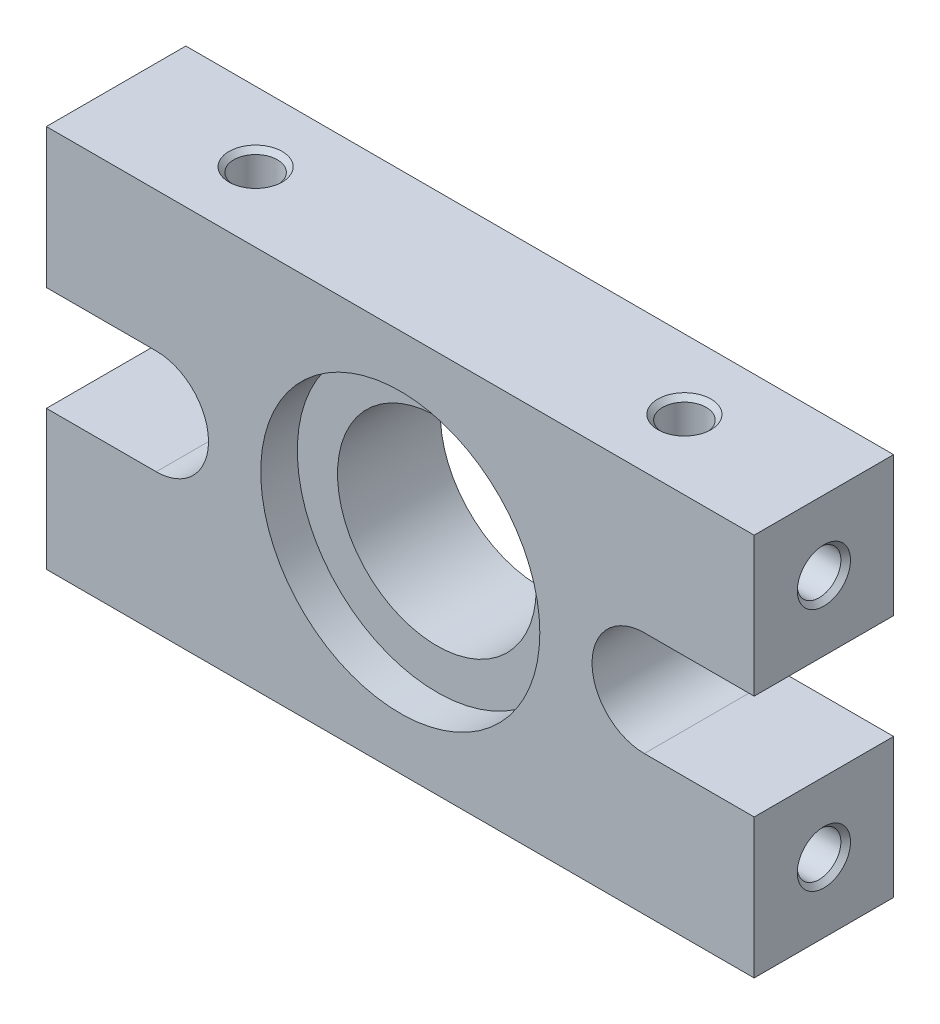
SolidWorks part; units mm, degrees
material "1060 Alloy"
ref_plane "Front Plane" through (0, 0, 0) normal (0, 0, 1) x (1, 0, 0)
ref_plane "Top Plane" through (0, 0, 0) normal (0, 1, 0) x (1, 0, 0)
ref_plane "Right Plane" through (0, 0, 0) normal (1, 0, 0) x (0, 0, -1)
sketch "Sketch1" plane through (0, 0, 0) normal (0, 0, 1) x (1, 0, 0)
  line L0 (0, 14) -> (0, 22)
  line L1 (0, 0) -> (40.6, 0)
  line L2 (0, 0) -> (0, 8)
  line L3 (0, 22) -> (40.6, 22)
  line L4 (40.6, 0) -> (40.6, 8)
  line L5 (0, 14) -> (6.3, 14)
  line L7 (0, 8) -> (6.3, 8)
  line L8 (40.6, 8) -> (34.3, 8)
  line L9 (40.6, 14) -> (34.3, 14)
  line L10 (40.6, 14) -> (40.6, 22)
  arc A0 (6.3, 8) -> (6.3, 14) centre (6.3, 11) ccw
  arc A1 (34.3, 8) -> (34.3, 14) centre (34.3, 11) cw
  circle A2 centre (20.3, 11) radius 5.7
  dimension "D3" = 6
  dimension "D5" = 11
  dimension "D7" = 11.4
  dimension "D1" = 40.6
  dimension "D2" = 22
  dimension "D4" = 6.3
  dimension "D6" = 6
extrude "Boss-Extrude1" add sketch "Sketch1" along normal blind 8
sketch "Sketch2" plane through (0, 0, 8) normal (0, 0, 1) x (1, 0, 0)
  circle A0 centre (20.3, 11) radius 8.005
  dimension "D1" = 16.01
extrude "Cut-Extrude1" cut sketch "Sketch2" against normal blind 2.1
ref_plane "Plane1" through (20.3, 0, 0) normal (1, 0, 0) x (0, 0, -1)
ref_plane "Plane2" through (0, 11, 0) normal (0, -1, 0) x (-1, 0, 0)
hole_wizard "M3x0.5 Tapped Hole1" positions "Sketch4" profile "Sketch3" tap size "M3x0.5" standard "ANSI Metric"
sketch "Sketch4" plane through (0, 22, 0) normal (0, 1, 0) x (1, 0, 0)
  line L0 (40.6, -8) -> (40.6, 0) construction
  line L1 (40.6, 0) -> (0, 0) construction
  point P0 (32.6, -4)
  dimension "D1" = 8
  dimension "D2" = 4
sketch "Sketch3" plane through (32.6, 22, 4) normal (1, 0, 0) x (0, 0, 1)
  line L0 (0, 0) -> (0, 5.7511)
  line L1 (0, 5.7511) -> (1.25, 5)
  line L2 (1.25, 5) -> (1.25, 0.275)
  line L3 (1.25, 0.275) -> (1.525, 0)
  line L5 (1.525, 0) -> (0, 0)
  line L6 (-1.25, 0.275) -> (-1.525, 0) construction
  line L10 (0, 5.7511) -> (-1.25, 5) construction
  line L11 (0, -6.35) -> (0, 107.95) construction
  dimension "Tap Drill Dia." = 2.5
  dimension "Tap Drill Depth" = 5
  dimension "Near C'Sink Dia." = 3.05
  dimension "Near C'Sink Angle" = 90
  dimension "Drill Angle" = 118
cosmetic thread "Hole Thread1" parameters "D1"=5, "D2"=3
mirror "Mirror1" about plane through (20.3, 0, 0) normal (1, 0, 0) of "M3x0.5 Tapped Hole1"
hole_wizard "M3x0.5 Tapped Hole2" positions "Sketch6" profile "Sketch5" tap size "M3x0.5" standard "ANSI Metric"
sketch "Sketch6" plane through (40.6, 0, 0) normal (1, 0, 0) x (0, 0, -1)
  line L0 (-8, 22) -> (0, 22) construction
  line L1 (-8, 14) -> (-8, 22) construction
  point P0 (-4, 18)
  dimension "D1" = 4
  dimension "D2" = 4
sketch "Sketch5" plane through (40.6, 18, 4) normal (0, 1, 0) x (0, 0, -1)
  line L0 (0, 0) -> (0, 7.2511)
  line L1 (0, 7.2511) -> (1.25, 6.5)
  line L2 (1.25, 6.5) -> (1.25, 0.275)
  line L3 (1.25, 0.275) -> (1.525, 0)
  line L5 (1.525, 0) -> (0, 0)
  line L6 (-1.25, 0.275) -> (-1.525, 0) construction
  line L10 (0, 7.2511) -> (-1.25, 6.5) construction
  line L11 (0, -6.35) -> (0, 107.95) construction
  dimension "Tap Drill Dia." = 2.5
  dimension "Tap Drill Depth" = 6.5
  dimension "Near C'Sink Dia." = 3.05
  dimension "Near C'Sink Angle" = 90
  dimension "Drill Angle" = 118
cosmetic thread "Hole Thread4" parameters "D1"=5, "D2"=3
mirror "Mirror2" about plane through (0, 11, 0) normal (0, -1, 0) of "M3x0.5 Tapped Hole2"
mirror "Mirror3" about plane through (20.3, 0, 0) normal (1, 0, 0) of "Mirror2", "M3x0.5 Tapped Hole2"
